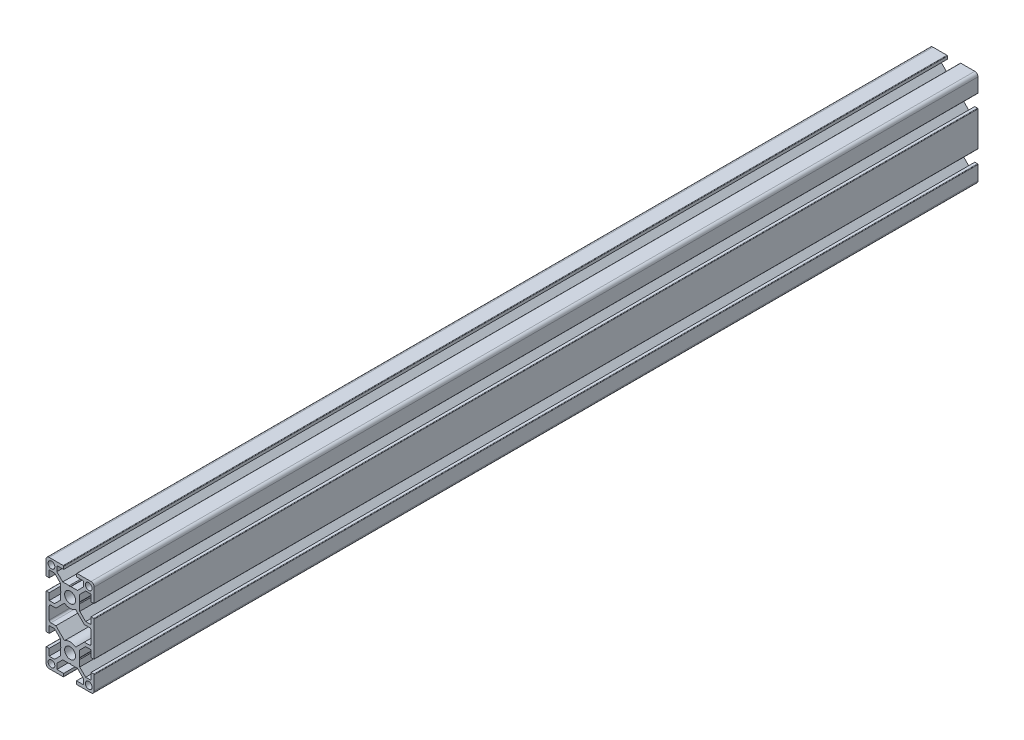
SolidWorks part; units mm, degrees
ref_plane "Front Plane" through (0, 0, 0) normal (0, 0, 1) x (1, 0, 0)
ref_plane "Top Plane" through (0, 0, 0) normal (0, 1, 0) x (1, 0, 0)
ref_plane "Right Plane" through (0, 0, 0) normal (1, 0, 0) x (0, 0, -1)
ref_plane "Plane1" through (0, 0, -1000) normal (0, 0, -1) x (-1, 0, 0)
sketch "Sketch1" plane through (0, 0, -1000) normal (0, 0, -1) x (-1, 0, 0)
  line L0 (13, 3.75) -> (13, -3.75)
  line L1 (12, -4.75) -> (8.8358, -4.75)
  line L2 (8.8358, -4.75) -> (3.4762, -10.1096)
  line L3 (-3.4762, -10.1096) -> (-8.8358, -4.75)
  line L4 (-8.8358, -4.75) -> (-12, -4.75)
  line L5 (-13, -3.75) -> (-13, 3.75)
  line L6 (-12, 4.75) -> (-8.8358, 4.75)
  line L7 (-8.8358, 4.75) -> (-3.4762, 10.1096)
  line L8 (3.4762, 10.1096) -> (8.8358, 4.75)
  line L9 (8.8358, 4.75) -> (12, 4.75)
  line L10 (15, -28) -> (15, -19.3)
  line L11 (14.7, -19) -> (13, -19)
  line L12 (13, -19) -> (13, -23.25)
  line L13 (13, -23.25) -> (9.6642, -23.25)
  line L14 (9.6642, -23.25) -> (6, -19.5858)
  line L15 (6, -19.5858) -> (6, -15.5196)
  line L16 (6, -15.5196) -> (5.7, -15)
  line L17 (5.7, -15) -> (6, -14.4804)
  line L18 (6, -14.4804) -> (6, -10.4142)
  line L19 (6, -10.4142) -> (9.6642, -6.75)
  line L20 (9.6642, -6.75) -> (13, -6.75)
  line L21 (13, -6.75) -> (13, -11)
  line L22 (13, -11) -> (14.7, -11)
  line L23 (15, -10.7) -> (15, 10.7)
  line L24 (14.7, 11) -> (13, 11)
  line L25 (13, 11) -> (13, 6.75)
  line L26 (13, 6.75) -> (9.6642, 6.75)
  line L27 (9.6642, 6.75) -> (6, 10.4142)
  line L28 (6, 10.4142) -> (6, 14.4804)
  line L29 (6, 14.4804) -> (5.7, 15)
  line L30 (5.7, 15) -> (6, 15.5196)
  line L31 (6, 15.5196) -> (6, 19.5858)
  line L32 (6, 19.5858) -> (9.6642, 23.25)
  line L33 (9.6642, 23.25) -> (13, 23.25)
  line L34 (13, 23.25) -> (13, 19)
  line L35 (13, 19) -> (14.7, 19)
  line L36 (15, 19.3) -> (15, 28)
  line L37 (13, 30) -> (4.3, 30)
  line L38 (4, 29.7) -> (4, 28)
  line L39 (4, 28) -> (8.25, 28)
  line L40 (8.25, 28) -> (8.25, 24.6642)
  line L41 (8.25, 24.6642) -> (4.5858, 21)
  line L42 (4.5858, 21) -> (0.5196, 21)
  line L43 (0.5196, 21) -> (0, 20.7)
  line L44 (0, 20.7) -> (-0.5196, 21)
  line L45 (-0.5196, 21) -> (-4.5858, 21)
  line L46 (-4.5858, 21) -> (-8.25, 24.6642)
  line L47 (-8.25, 24.6642) -> (-8.25, 28)
  line L48 (-8.25, 28) -> (-4, 28)
  line L49 (-4, 28) -> (-4, 29.7)
  line L50 (-4.3, 30) -> (-13, 30)
  line L51 (-15, 28) -> (-15, 19.3)
  line L52 (-14.7, 19) -> (-13, 19)
  line L53 (-13, 19) -> (-13, 23.25)
  line L54 (-13, 23.25) -> (-9.6642, 23.25)
  line L55 (-9.6642, 23.25) -> (-6, 19.5858)
  line L56 (-6, 19.5858) -> (-6, 15.5196)
  line L57 (-6, 15.5196) -> (-5.7, 15)
  line L58 (-5.7, 15) -> (-6, 14.4804)
  line L59 (-6, 14.4804) -> (-6, 10.4142)
  line L60 (-6, 10.4142) -> (-9.6642, 6.75)
  line L61 (-9.6642, 6.75) -> (-13, 6.75)
  line L62 (-13, 6.75) -> (-13, 11)
  line L63 (-13, 11) -> (-14.7, 11)
  line L64 (-15, 10.7) -> (-15, -10.7)
  line L65 (-14.7, -11) -> (-13, -11)
  line L66 (-13, -11) -> (-13, -6.75)
  line L67 (-13, -6.75) -> (-9.6642, -6.75)
  line L68 (-9.6642, -6.75) -> (-6, -10.4142)
  line L69 (-6, -10.4142) -> (-6, -14.4804)
  line L70 (-6, -14.4804) -> (-5.7, -15)
  line L71 (-5.7, -15) -> (-6, -15.5196)
  line L72 (-6, -15.5196) -> (-6, -19.5858)
  line L73 (-6, -19.5858) -> (-9.6642, -23.25)
  line L74 (-9.6642, -23.25) -> (-13, -23.25)
  line L75 (-13, -23.25) -> (-13, -19)
  line L76 (-13, -19) -> (-14.7, -19)
  line L77 (-15, -19.3) -> (-15, -28)
  line L78 (-13, -30) -> (-4.3, -30)
  line L79 (-4, -29.7) -> (-4, -28)
  line L80 (-4, -28) -> (-8.25, -28)
  line L81 (-8.25, -28) -> (-8.25, -24.6642)
  line L82 (-8.25, -24.6642) -> (-4.5858, -21)
  line L83 (-4.5858, -21) -> (-0.5196, -21)
  line L84 (-0.5196, -21) -> (0, -20.7)
  line L85 (0, -20.7) -> (0.5196, -21)
  line L86 (0.5196, -21) -> (4.5858, -21)
  line L87 (4.5858, -21) -> (8.25, -24.6642)
  line L88 (8.25, -24.6642) -> (8.25, -28)
  line L89 (8.25, -28) -> (4, -28)
  line L90 (4, -28) -> (4, -29.7)
  line L91 (4.3, -30) -> (13, -30)
  circle A0 centre (11.6, 26.625) radius 2.1
  circle A1 centre (11.6, -26.625) radius 2.1
  arc A2 (12, 4.75) -> (13, 3.75) centre (12, 3.75) cw
  arc A3 (13, -3.75) -> (12, -4.75) centre (12, -3.75) cw
  arc A4 (3.4762, -10.1096) -> (-3.4762, -10.1096) centre (0, -15) ccw
  arc A5 (-12, -4.75) -> (-13, -3.75) centre (-12, -3.75) cw
  arc A6 (-13, 3.75) -> (-12, 4.75) centre (-12, 3.75) cw
  arc A7 (-3.4762, 10.1096) -> (3.4762, 10.1096) centre (0, 15) ccw
  circle A8 centre (0, -15) radius 3.4
  circle A9 centre (0, 15) radius 3.4
  circle A10 centre (-11.6, 26.625) radius 2.1
  circle A11 centre (-11.6, -26.625) radius 2.1
  arc A12 (15, -19.3) -> (14.7, -19) centre (14.7, -19.3) ccw
  arc A13 (14.7, -11) -> (15, -10.7) centre (14.7, -10.7) ccw
  arc A14 (15, 10.7) -> (14.7, 11) centre (14.7, 10.7) ccw
  arc A15 (14.7, 19) -> (15, 19.3) centre (14.7, 19.3) ccw
  arc A16 (15, 28) -> (13, 30) centre (13, 28) ccw
  arc A17 (4.3, 30) -> (4, 29.7) centre (4.3, 29.7) ccw
  arc A18 (-4, 29.7) -> (-4.3, 30) centre (-4.3, 29.7) ccw
  arc A19 (-13, 30) -> (-15, 28) centre (-13, 28) ccw
  arc A20 (-15, 19.3) -> (-14.7, 19) centre (-14.7, 19.3) ccw
  arc A21 (-14.7, 11) -> (-15, 10.7) centre (-14.7, 10.7) ccw
  arc A22 (-15, -10.7) -> (-14.7, -11) centre (-14.7, -10.7) ccw
  arc A23 (-14.7, -19) -> (-15, -19.3) centre (-14.7, -19.3) ccw
  arc A24 (-15, -28) -> (-13, -30) centre (-13, -28) ccw
  arc A25 (-4.3, -30) -> (-4, -29.7) centre (-4.3, -29.7) ccw
  arc A26 (4, -29.7) -> (4.3, -30) centre (4.3, -29.7) ccw
  arc A27 (13, -30) -> (15, -28) centre (13, -28) ccw
extrude "Boss-Extrude1" add sketch "Sketch1" against normal blind 550
